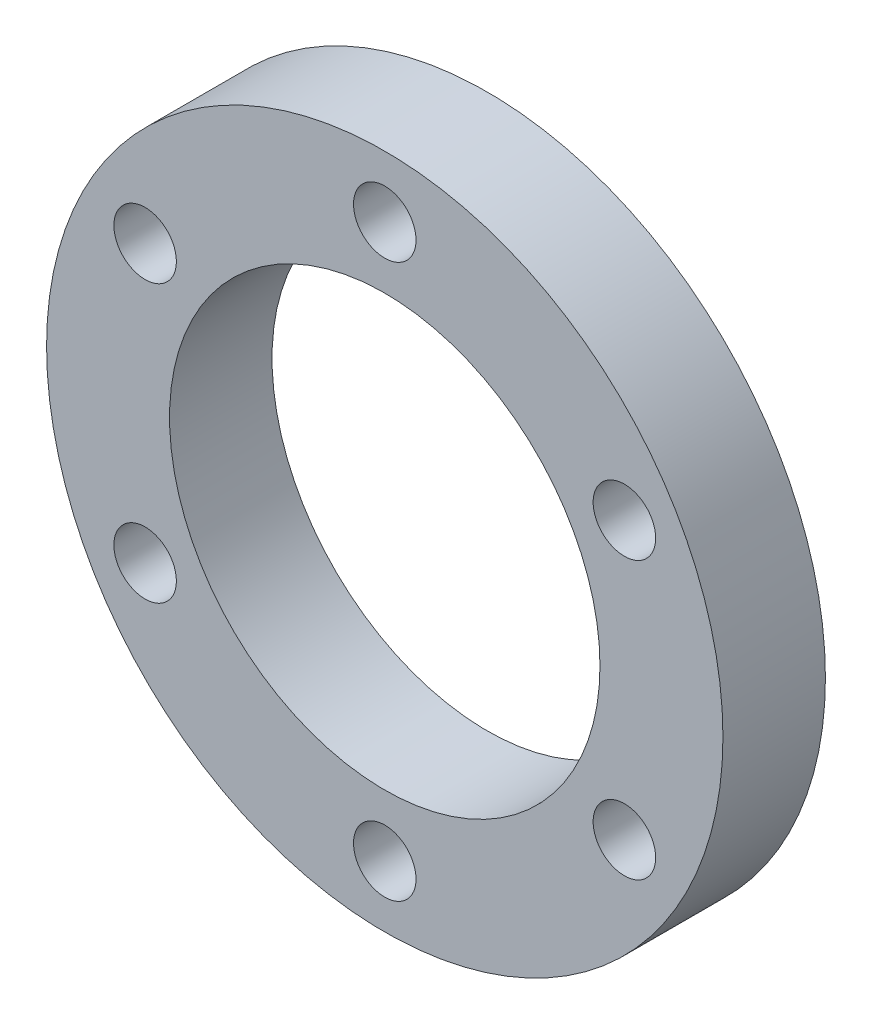
SolidWorks part; units mm, degrees
material "Thornel Mat VMA"
ref_plane "前视基准面" through (0, 0, 0) normal (0, 0, 1) x (1, 0, 0)
ref_plane "上视基准面" through (0, 0, 0) normal (0, 1, 0) x (1, 0, 0)
ref_plane "右视基准面" through (0, 0, 0) normal (1, 0, 0) x (0, 0, -1)
sketch "草图1" plane through (0, 0, 0) normal (0, 0, 1) x (1, 0, 0)
  circle A0 centre (0, 0) radius 13.5 construction
  circle A1 centre (0, 13.5) radius 1.525
  circle A2 centre (11.6913, 6.75) radius 1.525
  circle A3 centre (11.6913, -6.75) radius 1.525
  circle A4 centre (0, -13.5) radius 1.525
  circle A5 centre (-11.6913, -6.75) radius 1.525
  circle A6 centre (-11.6913, 6.75) radius 1.525
  circle A7 centre (0, 0) radius 10.5
  circle A8 centre (0, 0) radius 16.5
  point P17 (0, 0)
  dimension "D1" = 27
  dimension "D2" = 3.05
  dimension "D4" = 3
  dimension "D5" = 3
  dimension "D3" = 6
extrude "凸台-拉伸1" add sketch "草图1" along normal blind 5
